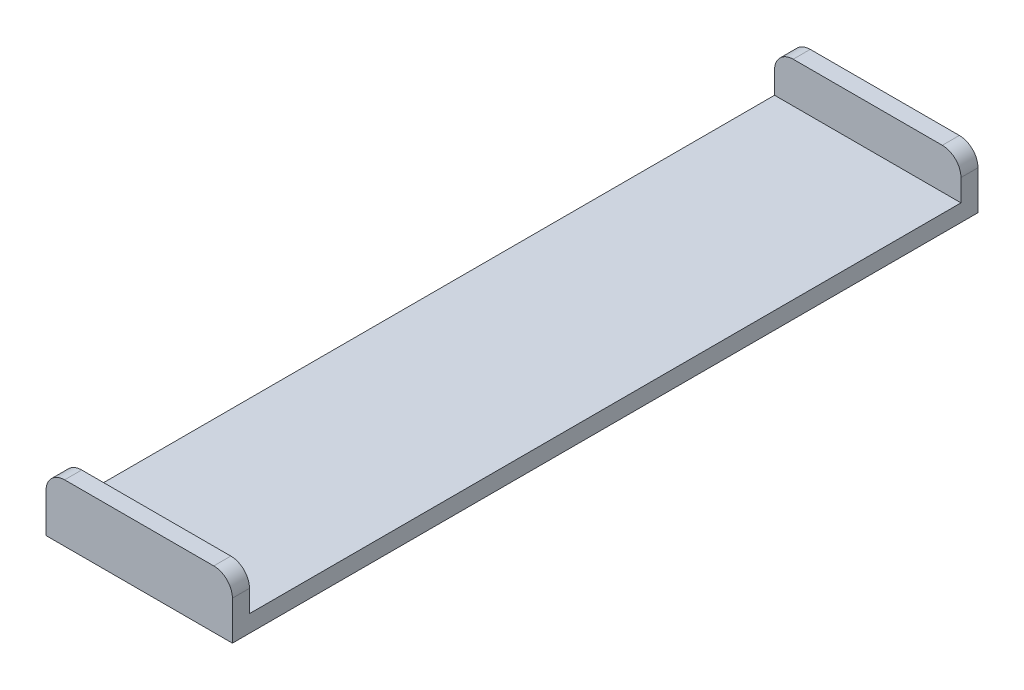
SolidWorks part; units mm, degrees
material "6061-T6 (SS)"
ref_plane "Front Plane" through (0, 0, 0) normal (0, 0, 1) x (1, 0, 0)
ref_plane "Top Plane" through (0, 0, 0) normal (0, 1, 0) x (1, 0, 0)
ref_plane "Right Plane" through (0, 0, 0) normal (1, 0, 0) x (0, 0, -1)
sketch "Sketch1" plane through (0, 0, 0) normal (0, 1, 0) x (1, 0, 0)
  line L1 (0, 0) -> (50.8, 0)
  line L2 (0, 0) -> (0, 203.2)
  line L3 (0, 203.2) -> (50.8, 203.2)
  line L4 (50.8, 0) -> (50.8, 203.2)
  dimension "D1" = 203.2
  dimension "D2" = 50.8
extrude "Boss-Extrude1" add sketch "Sketch1" along normal blind 4.6482
sketch "Sketch2" plane through (0, 4.6482, 0) normal (0, 1, 0) x (1, 0, 0)
  line L0 (50.8, 0) -> (50.8, 203.2) construction
  line L1 (0, 0) -> (50.8, 0)
  line L2 (0, 0) -> (0, 4.6482)
  line L3 (0, 4.6482) -> (50.8, 4.6482)
  line L4 (50.8, 0) -> (50.8, 4.6482)
  line L6 (0, 203.2) -> (50.8, 203.2)
  line L7 (0, 203.2) -> (0, 198.5518)
  line L8 (0, 198.5518) -> (50.8, 198.5518)
  line L9 (50.8, 203.2) -> (50.8, 198.5518)
  dimension "D1" = 4.6482
  dimension "D2" = 4.6482
extrude "Boss-Extrude2" add sketch "Sketch2" along normal blind 11.049
fillet "Fillet1" radius 5.08 4 edges at (50.8, 15.6972, -200.8759) (0, 15.6972, -200.8759) (0, 15.6972, -2.3241) (50.8, 15.6972, -2.3241)
